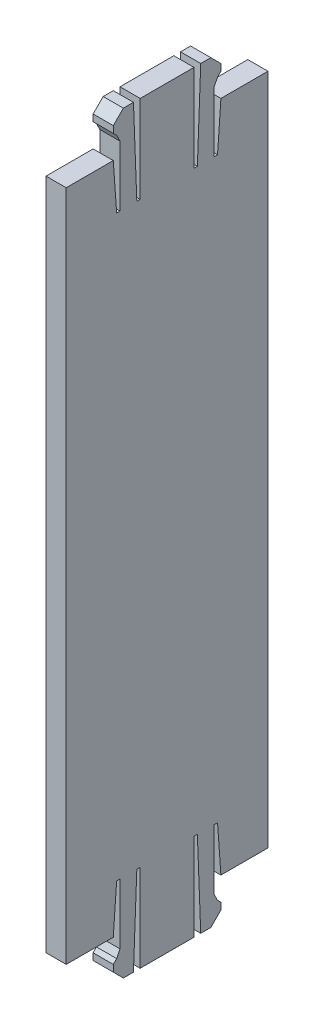
SolidWorks part; units mm, degrees
ref_plane "Front Plane" through (0, 0, 0) normal (0, 0, 1) x (1, 0, 0)
ref_plane "Top Plane" through (0, 0, 0) normal (0, 1, 0) x (1, 0, 0)
ref_plane "Right Plane" through (0, 0, 0) normal (1, 0, 0) x (0, 0, -1)
sketch "Sketch1" plane through (0, 0, 0) normal (1, 0, 0) x (0, 0, -1)
  line L0 (-15, -50) -> (-8, -50)
  line L1 (8, -50) -> (15, -50)
  line L2 (-15, -50) -> (-15, 50)
  line L3 (8, 50) -> (15, 50)
  line L4 (15, -50) -> (15, 50)
  line L5 (-15, -50) -> (15, 50) construction
  line L6 (-15, 50) -> (15, -50) construction
  line L7 (8, -50) -> (7.5, -42.9978)
  line L8 (7.5, -42.9978) -> (7, -42.9978)
  line L9 (7, -42.9978) -> (7, -51.9978)
  line L10 (7, -51.9978) -> (7.5, -52.9978)
  line L11 (7.5, -52.9978) -> (8, -53.4978)
  line L12 (8, -53.4978) -> (8, -54.4978)
  line L13 (8, -54.4978) -> (6.5, -55.9978)
  line L14 (6.5, -55.9978) -> (5, -55.9978)
  line L15 (5, -55.9978) -> (4.5, -42.9978)
  line L16 (4.5, -42.9978) -> (4, -42.9978)
  line L17 (4, -42.9978) -> (4, -55.9978)
  line L18 (0, -50) -> (0, -55.7386) construction
  line L19 (-4, -42.9978) -> (-4, -55.9978)
  line L20 (-4.5, -42.9978) -> (-4, -42.9978)
  line L21 (-5, -55.9978) -> (-4.5, -42.9978)
  line L22 (-6.5, -55.9978) -> (-5, -55.9978)
  line L23 (-8, -54.4978) -> (-6.5, -55.9978)
  line L24 (-8, -53.4978) -> (-8, -54.4978)
  line L25 (-7.5, -52.9978) -> (-8, -53.4978)
  line L26 (-7, -51.9978) -> (-7.5, -52.9978)
  line L27 (-7, -42.9978) -> (-7, -51.9978)
  line L28 (-7.5, -42.9978) -> (-7, -42.9978)
  line L29 (-8, -50) -> (-7.5, -42.9978)
  line L30 (4, -55.9978) -> (-4, -55.9978)
  line L31 (-8, 50) -> (-15, 50)
  line L32 (-8, 50) -> (-7.5, 42.9978)
  line L33 (-7.5, 42.9978) -> (-7, 42.9978)
  line L34 (-7, 42.9978) -> (-7, 51.9978)
  line L35 (-7, 51.9978) -> (-7.5, 52.9978)
  line L36 (-7.5, 52.9978) -> (-8, 53.4978)
  line L37 (-8, 53.4978) -> (-8, 54.4978)
  line L38 (-8, 54.4978) -> (-6.5, 55.9978)
  line L39 (-6.5, 55.9978) -> (-5, 55.9978)
  line L40 (-5, 55.9978) -> (-4.5, 42.9978)
  line L41 (-4.5, 42.9978) -> (-4, 42.9978)
  line L42 (-4, 42.9978) -> (-4, 55.9978)
  line L43 (0, 50) -> (0, 55.7386) construction
  line L44 (4, 42.9978) -> (4, 55.9978)
  line L45 (4.5, 42.9978) -> (4, 42.9978)
  line L46 (5, 55.9978) -> (4.5, 42.9978)
  line L47 (6.5, 55.9978) -> (5, 55.9978)
  line L48 (8, 54.4978) -> (6.5, 55.9978)
  line L49 (8, 53.4978) -> (8, 54.4978)
  line L50 (7.5, 52.9978) -> (8, 53.4978)
  line L51 (7, 51.9978) -> (7.5, 52.9978)
  line L52 (7, 42.9978) -> (7, 51.9978)
  line L53 (7.5, 42.9978) -> (7, 42.9978)
  line L54 (8, 50) -> (7.5, 42.9978)
  line L55 (-4, 55.9978) -> (4, 55.9978)
  point P0 (0, 0)
  point P10 (0, -50)
  point P11 (8, -50)
  point P12 (-8, -50)
  point P13 (-8, -50)
  point P40 (-8, 50)
  dimension "D1" = 100
  dimension "D2" = 30
  dimension "D3" = 7
  dimension "D4" = 7
  dimension "D5" = 8
  dimension "D6" = 0.5
  dimension "D7" = 9
  dimension "D8" = 0.5
  dimension "D9" = 1
  dimension "D10" = 0.5
  dimension "D11" = 0.5
  dimension "D12" = 1
  dimension "D13" = 1.5
  dimension "D14" = 1.5
  dimension "D15" = 0.5
  dimension "D16" = 0.5
  dimension "D17" = 13
  dimension "D18" = 7.0022
  dimension "D19" = 0.5
  dimension "D20" = 1.5
  dimension "D21" = 13
  dimension "D22" = 8
  dimension "D23" = 0.5
  dimension "D24" = 9
  dimension "D25" = 0.5
  dimension "D26" = 1
  dimension "D27" = 0.5
  dimension "D28" = 0.5
  dimension "D29" = 1
  dimension "D30" = 1.5
  dimension "D31" = 1.5
  dimension "D32" = 0.5
  dimension "D33" = 0.5
  dimension "D34" = 13
  dimension "D35" = 7.0022
  dimension "D36" = 0.5
  dimension "D37" = 1.5
  dimension "D38" = 13
  dimension "D39" = 8
  dimension "D40" = 8
extrude "Boss-Extrude1" add sketch "Sketch1" along normal blind 3
sketch "Sketch2" plane through (3, 0, 0) normal (1, 0, 0) x (0, 0, -1)
  text T0 "STABILITY"
  dimension "D1" = 1.5988
  dimension "D2" = 9.4
